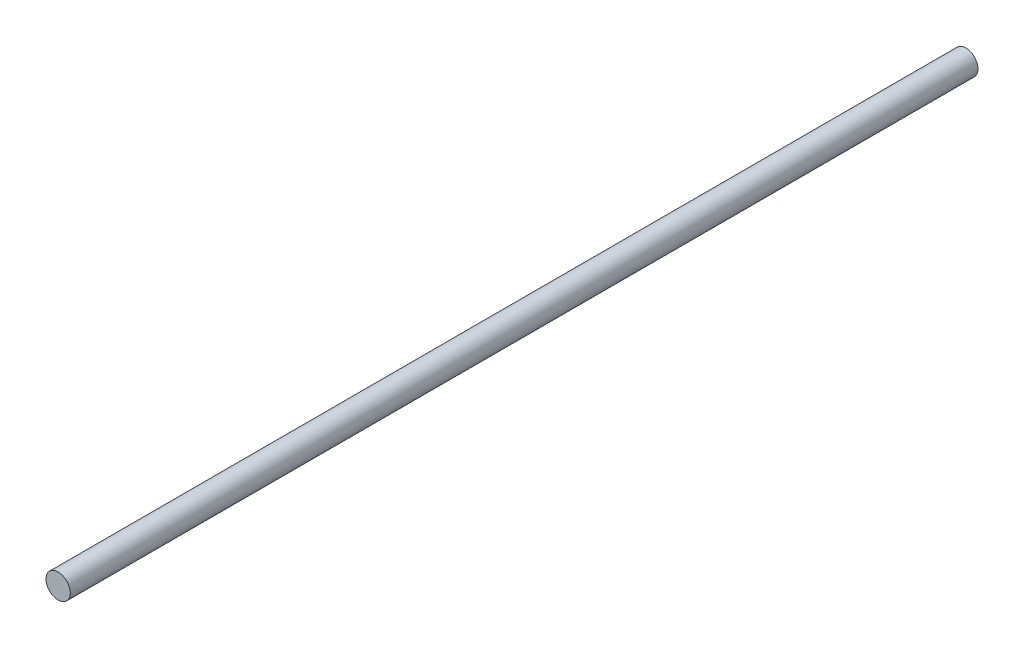
SolidWorks part; units mm, degrees
material "201 Annealed Stainless Steel (SS)"
ref_plane "Front Plane" through (0, 0, 0) normal (0, 0, 1) x (1, 0, 0)
ref_plane "Top Plane" through (0, 0, 0) normal (0, 1, 0) x (1, 0, 0)
ref_plane "Right Plane" through (0, 0, 0) normal (1, 0, 0) x (0, 0, -1)
sketch "Sketch1" plane through (0, 0, 0) normal (0, 0, 1) x (1, 0, 0)
  circle A0 centre (0, 0) radius 2.3813
  dimension "D1" = 4.7625
extrude "Boss-Extrude1" add sketch "Sketch1" along normal blind 177.8
sketch "Sketch2" plane through (0, 0, 0) normal (0, 0, -1) x (-1, 0, 0)
  circle A0 centre (0, 0) radius 1.5875
  circle A1 centre (0, 0) radius 2.3813
  dimension "D1" = 3.175
extrude "Cut-Extrude1" [suppressed] cut sketch "Sketch2" against normal blind 12.7
sketch "Sketch3" plane through (0, 0, 177.8) normal (0, 0, 1) x (1, 0, 0)
  circle A0 centre (0, 0) radius 1.5875
  circle A1 centre (0, 0) radius 2.3813
  dimension "D1" = 3.175
extrude "Cut-Extrude2" [suppressed] cut sketch "Sketch3" against normal blind 12.7
